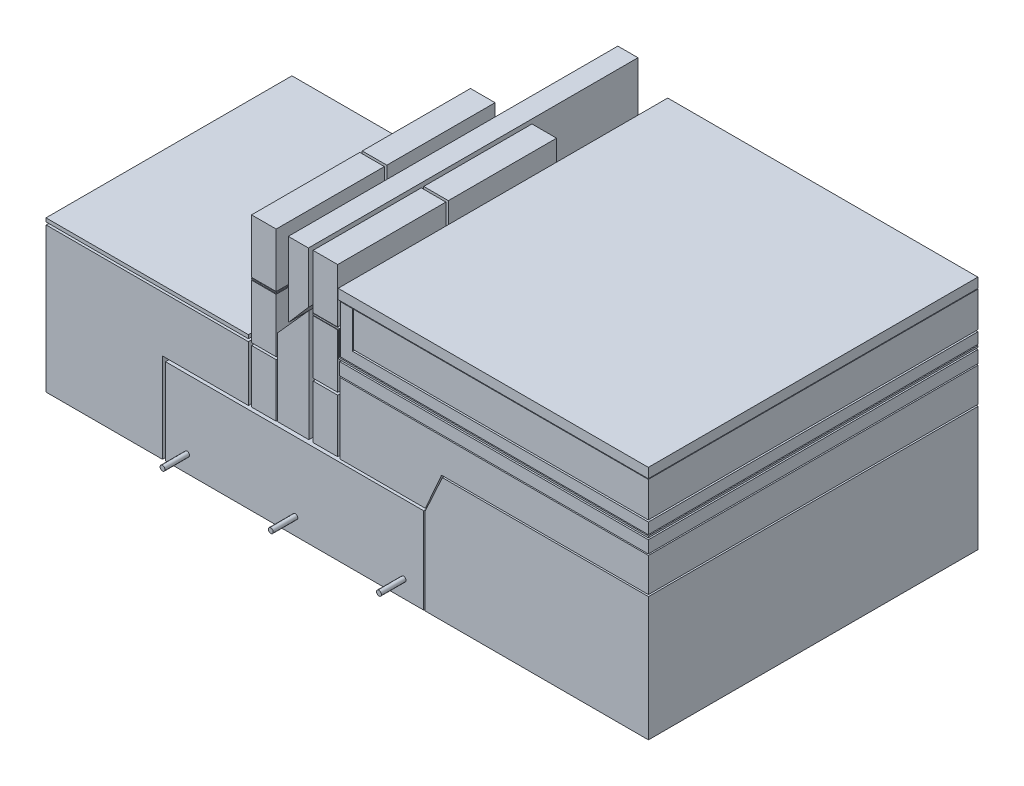
SolidWorks part; units mm, degrees
ref_plane "Front" through (0, 0, 0) normal (0, 0, 1) x (1, 0, 0)
ref_plane "Top" through (0, 0, 0) normal (0, 1, 0) x (1, 0, 0)
ref_plane "Right" through (0, 0, 0) normal (1, 0, 0) x (0, 0, -1)
sketch "Sketch1" plane through (0, 0, 0) normal (0, 0, 1) x (1, 0, 0)
  line L1 (0, 0) -> (-1050, 0)
  line L2 (0, 0) -> (0, 350)
  line L3 (0, 350) -> (-1050, 350)
  line L4 (-1050, 0) -> (-1050, 350)
  dimension "D1" = 1050
  dimension "D2" = 350
extrude "Extrude1" add sketch "Sketch1" against normal blind 1500
sketch "Sketch2" plane through (0, 0, 0) normal (0, 0, 1) x (1, 0, 0)
  line L0 (0, 0) -> (0, 350) construction
  line L1 (-700, 365.1993) -> (-600, 365.1993)
  line L2 (-700, 365.1993) -> (-700, 582.0932)
  line L3 (-700, 582.0932) -> (-600, 582.0932)
  line L4 (-600, 365.1993) -> (-600, 582.0932)
  line L5 (-450, 365.1993) -> (-350, 365.1993)
  line L6 (-450, 365.1993) -> (-450, 582.0932)
  line L7 (-450, 582.0932) -> (-350, 582.0932)
  line L8 (-350, 365.1993) -> (-350, 582.0932)
  dimension "D1" = 150
  dimension "D2" = 100
  dimension "D3" = 100
  dimension "D4" = 350
extrude "Extrude2" add sketch "Sketch2" against normal blind 440 separate body
sketch "Sketch3" plane through (-700, 0, 0) normal (-1, 0, 0) x (0, 0, 1)
  line L0 (-440, 582.0932) -> (-440, 365.1993) construction
  line L1 (-450, 582.0932) -> (-890, 582.0932)
  line L2 (-450, 582.0932) -> (-450, 362.0932)
  line L3 (-450, 362.0932) -> (-890, 362.0932)
  line L4 (-890, 582.0932) -> (-890, 362.0932)
  line L6 (-900, 582.0932) -> (-1340, 582.0932)
  line L7 (-900, 582.0932) -> (-900, 362.0932)
  line L8 (-900, 362.0932) -> (-1340, 362.0932)
  line L9 (-1340, 582.0932) -> (-1340, 362.0932)
  dimension "D1" = 440
  dimension "D2" = 220
  dimension "D3" = 10
  dimension "D4" = 440
  dimension "D5" = 220
  dimension "D6" = 10
extrude "Extrude3" add sketch "Sketch3" against normal blind 100 separate body
sketch "Sketch4" plane through (-350, 0, 0) normal (1, 0, 0) x (0, 0, -1)
  line L1 (450, 582.0932) -> (890, 582.0932)
  line L2 (450, 582.0932) -> (450, 362.0932)
  line L3 (450, 362.0932) -> (890, 362.0932)
  line L4 (890, 582.0932) -> (890, 362.0932)
  line L5 (1340, 582.0932) -> (900, 582.0932)
  line L6 (1340, 582.0932) -> (1340, 362.0932)
  line L7 (1340, 362.0932) -> (900, 362.0932)
  line L8 (900, 582.0932) -> (900, 362.0932)
extrude "Extrude4" add sketch "Sketch4" against normal blind 100 separate body
sketch "Sketch6" plane through (-700, 0, 0) normal (-1, 0, 0) x (0, 0, 1)
  line L0 (-440, 582.0932) -> (0, 582.0932) construction
  line L1 (0, 592.0932) -> (-215, 592.0932)
  line L2 (0, 592.0932) -> (0, 812.0932)
  line L3 (0, 812.0932) -> (-215, 812.0932)
  line L4 (-215, 592.0932) -> (-215, 812.0932)
  line L5 (0, 582.0932) -> (0, 365.1993) construction
  line L6 (-225, 812.0932) -> (-670.705, 812.0932)
  line L7 (-225, 812.0932) -> (-225, 592.0932)
  line L8 (-225, 592.0932) -> (-670.705, 592.0932)
  line L9 (-670.705, 812.0932) -> (-670.705, 592.0932)
  line L11 (-680.705, 812.0932) -> (-1120.705, 812.0932)
  line L12 (-680.705, 812.0932) -> (-680.705, 592.0932)
  line L13 (-680.705, 592.0932) -> (-1120.705, 592.0932)
  line L14 (-1120.705, 812.0932) -> (-1120.705, 592.0932)
  dimension "D1" = 215
  dimension "D2" = 220
  dimension "D3" = 10
  dimension "D4" = 445.705
  dimension "D5" = 10
  dimension "D6" = 440
  dimension "D7" = 220
  dimension "D8" = 10
extrude "Extrude6" add sketch "Sketch6" against normal blind 100 separate body
sketch "Sketch7" plane through (-350, 0, 0) normal (1, 0, 0) x (0, 0, -1)
  line L1 (0, 812.0932) -> (215, 812.0932)
  line L2 (0, 812.0932) -> (0, 592.0932)
  line L3 (0, 592.0932) -> (215, 592.0932)
  line L4 (215, 812.0932) -> (215, 592.0932)
  line L5 (670.705, 812.0932) -> (225, 812.0932)
  line L6 (670.705, 812.0932) -> (670.705, 592.0932)
  line L7 (670.705, 592.0932) -> (225, 592.0932)
  line L8 (225, 812.0932) -> (225, 592.0932)
  line L9 (1120.705, 812.0932) -> (680.705, 812.0932)
  line L10 (1120.705, 812.0932) -> (1120.705, 592.0932)
  line L11 (1120.705, 592.0932) -> (680.705, 592.0932)
  line L12 (680.705, 812.0932) -> (680.705, 592.0932)
extrude "Extrude7" add sketch "Sketch7" against normal blind 100 separate body
sketch "Sketch8" plane through (-700, 0, 0) normal (-1, 0, 0) x (0, 0, 1)
  line L1 (0, 822.0932) -> (-440, 822.0932)
  line L2 (0, 822.0932) -> (0, 1042.0932)
  line L3 (0, 1042.0932) -> (-440, 1042.0932)
  line L4 (-440, 822.0932) -> (-440, 1042.0932)
  line L5 (-450, 1042.0932) -> (-890, 1042.0932)
  line L6 (-450, 1042.0932) -> (-450, 822.0932)
  line L7 (-450, 822.0932) -> (-890, 822.0932)
  line L8 (-890, 1042.0932) -> (-890, 822.0932)
  line L9 (0, 592.0932) -> (0, 812.0932) construction
  line L10 (-225, 812.0932) -> (-670.705, 812.0932) construction
  dimension "D1" = 220
  dimension "D2" = 440
  dimension "D3" = 440
  dimension "D4" = 220
  dimension "D5" = 10
  dimension "D6" = 10
extrude "Extrude8" add sketch "Sketch8" against normal blind 100 separate body
sketch "Sketch9" plane through (-350, 0, 0) normal (1, 0, 0) x (0, 0, -1)
  line L0 (450, 822.0932) -> (450, 1042.0932) construction
  line L1 (0, 1042.0932) -> (440, 1042.0932)
  line L2 (0, 1042.0932) -> (0, 822.0932)
  line L3 (0, 822.0932) -> (440, 822.0932)
  line L4 (440, 1042.0932) -> (440, 822.0932)
  line L5 (890, 1042.0932) -> (450, 1042.0932)
  line L6 (890, 1042.0932) -> (890, 822.0932)
  line L7 (890, 822.0932) -> (450, 822.0932)
  line L8 (450, 1042.0932) -> (450, 822.0932)
  line L9 (890, 822.0932) -> (450, 822.0932) construction
extrude "Extrude9" add sketch "Sketch9" against normal blind 100 separate body
sketch "Sketch10" plane through (0, 0, 0) normal (0, 0, 1) x (1, 0, 0)
  circle A0 centre (-962.1446, 68.9019) radius 10
  circle A1 centre (-522.1446, 68.9019) radius 10
  circle A2 centre (-82.1446, 68.9019) radius 10
  dimension "D1" = 20
  dimension "D2" = 20
  dimension "D3" = 20
  dimension "D4" = 440
  dimension "D5" = 440
extrude "Extrude10" add sketch "Sketch10" along normal blind 100
sketch "Sketch11" plane through (0, 0, 0) normal (0, 0, 1) x (1, 0, 0)
  line L0 (-467.1426, 366.7602) -> (-467.1426, 821.0478)
  line L1 (-467.1426, 821.0478) -> (-593.7131, 680.0214)
  line L2 (-593.7131, 680.0214) -> (-593.7131, 366.7602)
  line L3 (-593.7131, 366.7602) -> (-467.1426, 366.7602)
extrude "Extrude11" add sketch "Sketch11" against normal up to vertex (1340 mm away) separate body
sketch "Sketch12" plane through (0, 0, 0) normal (0, 0, 1) x (1, 0, 0)
  line L0 (-468.8878, 831.9878) -> (-468.8878, 1040.9897)
  line L1 (-468.8878, 1040.9897) -> (-550.7167, 1040.9897)
  line L2 (-550.7167, 1040.9897) -> (-550.7167, 737.6058)
  line L3 (-550.7167, 737.6058) -> (-468.8878, 831.9878)
extrude "Extrude12" add sketch "Sketch12" against normal up to vertex (1340 mm away) separate body
sketch "Sketch13" plane through (0, 0, 0) normal (0, 0, 1) x (1, 0, 0)
  line L1 (6.5399, 361.9862) -> (72.3728, 511.6205)
  line L2 (72.3728, 511.6205) -> (913.6669, 511.6205)
  line L3 (913.6669, 511.6205) -> (913.6669, 649.5375)
  line L4 (913.6669, 649.5375) -> (-341.3783, 649.5375)
  line L5 (-341.3783, 649.5375) -> (-341.3783, 361.9862)
  line L6 (-341.3783, 361.9862) -> (6.5399, 361.9862)
extrude "Extrude13" add sketch "Sketch13" against normal up to vertex (1340 mm away) separate body
sketch "Sketch15" plane through (0, 0, 0) normal (0, 0, 1) x (1, 0, 0)
  line L0 (913.6669, 649.5375) -> (-341.3783, 649.5375) construction
  line L1 (-341.4883, 654.5375) -> (913.1329, 654.5375)
  line L2 (-341.4883, 654.5375) -> (-341.4883, 704.5211)
  line L3 (-341.4883, 704.5211) -> (913.1329, 704.5211)
  line L4 (913.1329, 654.5375) -> (913.1329, 704.5211)
  dimension "D1" = 5
extrude "Extrude23" add sketch "Sketch15" against normal up to vertex (1340 mm away) separate body
sketch "Sketch19" plane through (0, 0, 0) normal (0, 0, 1) x (1, 0, 0)
  line L1 (-600.0803, 819.7616) -> (-700.0973, 819.7616)
  line L2 (-600.0803, 819.7616) -> (-600.0803, 815.3456)
  line L3 (-600.0803, 815.3456) -> (-700.0973, 815.3456)
  line L4 (-700.0973, 819.7616) -> (-700.0973, 815.3456)
extrude "Extrude19" add sketch "Sketch19" against normal up to vertex (1120.705 mm away) separate body
sketch "Sketch20" plane through (0, 0, 0) normal (0, 0, 1) x (1, 0, 0)
  line L0 (-712.8633, 364.1535) -> (-712.8633, 588.9022)
  line L1 (-712.8633, 588.9022) -> (-1535.1127, 588.9022)
  line L2 (-1535.1127, 588.9022) -> (-1535.1127, 0)
  line L3 (-1535.1127, 0) -> (-1062.5026, 0)
  line L4 (-1062.5026, 0) -> (-1062.5026, 364.1535)
  line L5 (-1062.5026, 364.1535) -> (-712.8633, 364.1535)
extrude "Extrude20" add sketch "Sketch20" against normal blind 1000 separate body
sketch "Sketch21" plane through (0, 0, 0) normal (0, 0, 1) x (1, 0, 0)
  line L0 (-712.8633, 599.2947) -> (-712.8633, 613.7286)
  line L1 (-712.8633, 613.7286) -> (-1535.8842, 613.7286)
  line L2 (-1535.8842, 613.7286) -> (-1535.8842, 599.2947)
  line L3 (-1535.8842, 599.2947) -> (-712.8633, 599.2947)
extrude "Extrude21" add sketch "Sketch21" against normal up to vertex (1000 mm away) separate body
sketch "Sketch22" plane through (0, 0, 0) normal (0, 0, 1) x (1, 0, 0)
  line L0 (5.3443, 0) -> (5.3443, 350.3409)
  line L1 (5.3443, 350.3409) -> (75.9471, 504.6375)
  line L2 (75.9471, 504.6375) -> (913.6669, 504.6375)
  line L3 (913.6669, 504.6375) -> (913.6669, 0)
  line L4 (913.6669, 0) -> (5.3443, 0)
extrude "Extrude22" add sketch "Sketch22" against normal up to vertex (1340 mm away) separate body
sketch "Sketch23" plane through (0, 0, 0) normal (0, 0, 1) x (1, 0, 0)
  line L0 (-450.3245, 820.4658) -> (-342.5881, 820.4658)
  line L1 (-342.5881, 820.4658) -> (-342.5881, 718.3194)
  line L2 (-342.5881, 718.3194) -> (913.1329, 718.3194)
  line L3 (913.1329, 718.3194) -> (913.1329, 711.1487)
  line L4 (913.1329, 711.1487) -> (-346.6352, 711.1487)
  line L5 (-346.6352, 711.1487) -> (-346.6352, 814.0263)
  line L6 (-346.6352, 814.0263) -> (-450.3245, 814.0263)
  line L7 (-450.3245, 814.0263) -> (-450.3245, 820.4658)
extrude "Extrude24" add sketch "Sketch23" against normal up to vertex (1340 mm away) separate body
sketch "Sketch24" plane through (0, 0, 0) normal (0, 0, 1) x (1, 0, 0)
  line L0 (-289.0315, 766.948) -> (-289.0315, 916.948)
  line L1 (-289.0315, 916.948) -> (-339.1718, 916.948)
  line L2 (-339.1718, 916.948) -> (-339.1718, 722.492)
  line L3 (-289.0315, 766.948) -> (913.1329, 766.948)
  line L4 (913.1329, 766.948) -> (913.1329, 722.492)
  line L5 (913.1329, 722.492) -> (-339.1718, 722.492)
  dimension "D1" = 150
extrude "Extrude25" add sketch "Sketch24" against normal up to vertex (1340 mm away) separate body
sketch "Sketch25" plane through (0, 0, 0) normal (0, 0, 1) x (1, 0, 0)
  line L1 (-285.9936, 916.948) -> (913.1329, 916.948)
  line L2 (-285.9936, 916.948) -> (-285.9936, 774.3267)
  line L3 (-285.9936, 774.3267) -> (913.1329, 774.3267)
  line L4 (913.1329, 916.948) -> (913.1329, 774.3267)
extrude "Extrude26" add sketch "Sketch25" against normal up to vertex (1340 mm away) separate body
sketch "Sketch26" plane through (0, 0, -1340) normal (0, 0, -1) x (-1, 0, 0)
  line L1 (347.9787, 919.4874) -> (-913.1329, 919.4874)
  line L2 (347.9787, 919.4874) -> (347.9787, 959.4874)
  line L3 (347.9787, 959.4874) -> (-913.1329, 959.4874)
  line L4 (-913.1329, 919.4874) -> (-913.1329, 959.4874)
  dimension "D1" = 40
extrude "Extrude28" add sketch "Sketch26" against normal up to vertex (1340 mm away) separate body
